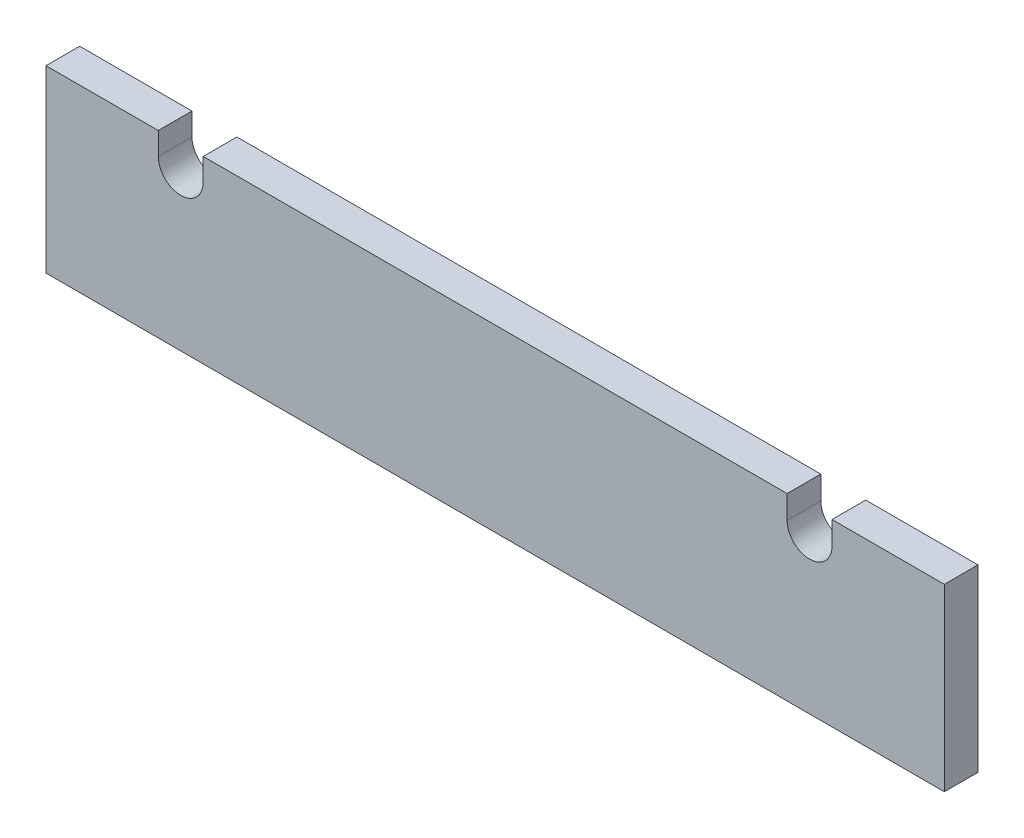
SolidWorks part; units mm, degrees
material "Oak"
ref_plane "Front Plane" through (0, 0, 0) normal (0, 0, 1) x (1, 0, 0)
ref_plane "Top Plane" through (0, 0, 0) normal (0, 1, 0) x (1, 0, 0)
ref_plane "Right Plane" through (0, 0, 0) normal (1, 0, 0) x (0, 0, -1)
sketch "Sketch1" plane through (0, 0, 0) normal (0, 0, 1) x (1, 0, 0)
  line L0 (88.9, 88.9) -> (419.1, 88.54) construction
  line L1 (0, 0) -> (508, 0)
  line L2 (0, 0) -> (0, 101.6)
  line L3 (0, 101.6) -> (508, 101.6)
  line L4 (508, 0) -> (508, 101.6)
  line L5 (63.5, 88.9) -> (88.9, 88.9)
  line L6 (63.5, 88.9) -> (63.5, 101.6)
  line L7 (63.5, 101.6) -> (88.9, 101.6)
  line L8 (88.9, 88.9) -> (88.9, 101.6)
  line L9 (419.1, 101.6) -> (444.5, 101.6)
  line L10 (419.1, 101.6) -> (419.1, 88.54)
  line L11 (419.1, 88.54) -> (444.5, 88.54)
  line L12 (444.5, 101.6) -> (444.5, 88.54)
  circle A0 centre (76.2, 88.9) radius 12.7
  circle A1 centre (431.8, 88.54) radius 12.7
  point P13 (254, 88.72)
  point P18 (254, 101.6)
  dimension "D3" = 25.4
  dimension "D4" = 355.6
  dimension "D1" = 101.6
  dimension "D2" = 508
  dimension "D5" = 12.7
extrude "Boss-Extrude1" add sketch "Sketch1" along normal blind 19.05 contours A1 L10 L3 L8 A0 L6 L2 L1 L4 L12 | L8 L0 L10 L3
